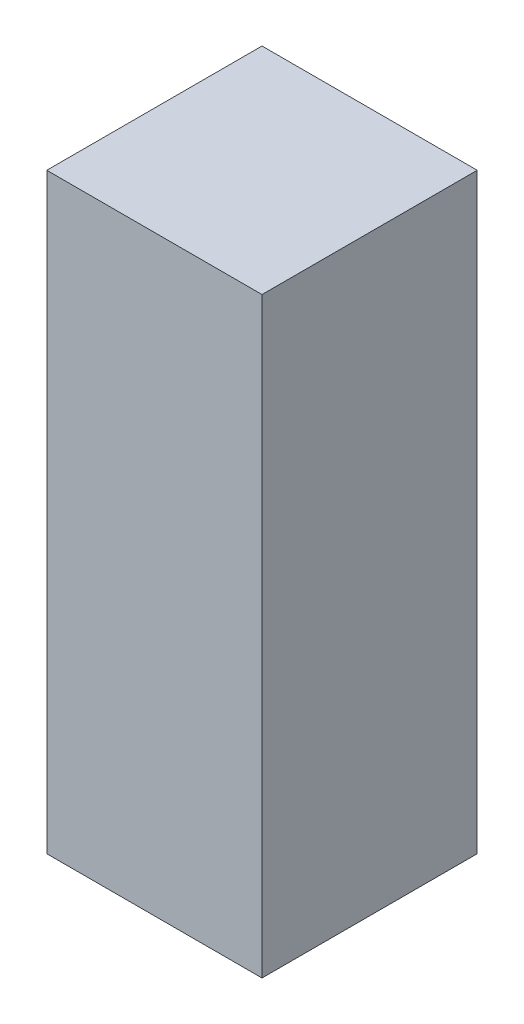
SolidWorks part; units mm, degrees
ref_plane "Front Plane" through (0, 0, 0) normal (0, 0, 1) x (1, 0, 0)
ref_plane "Top Plane" through (0, 0, 0) normal (0, 1, 0) x (1, 0, 0)
ref_plane "Right Plane" through (0, 0, 0) normal (1, 0, 0) x (0, 0, -1)
sketch "Sketch1" plane through (0, 0, 0) normal (0, 1, 0) x (1, 0, 0)
  line L1 (-20, 20) -> (20, 20)
  line L2 (-20, 20) -> (-20, -20)
  line L3 (-20, -20) -> (20, -20)
  line L4 (20, 20) -> (20, -20)
  line L5 (-20, 20) -> (20, -20) construction
  line L6 (-20, -20) -> (20, 20) construction
  point P0 (0, 0)
  dimension "D1" = 40
  dimension "D2" = 40
extrude "Boss-Extrude1" add sketch "Sketch1" along normal blind 110
